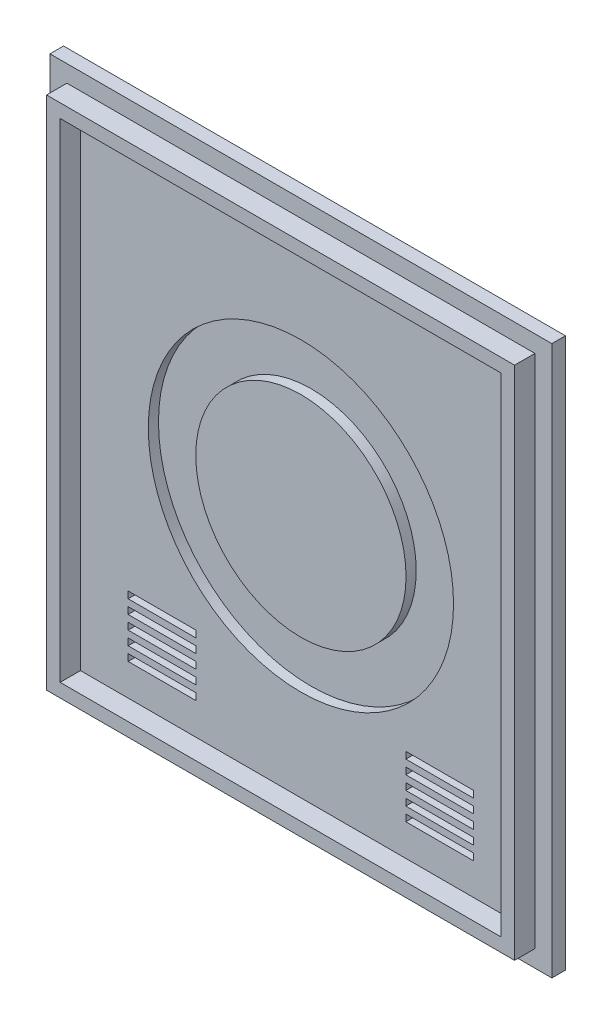
SolidWorks part; units mm, degrees
ref_plane "Ebene vorne" through (0, 0, 0) normal (0, 0, 1) x (1, 0, 0)
ref_plane "Ebene oben" through (0, 0, 0) normal (0, 1, 0) x (1, 0, 0)
ref_plane "Ebene rechts" through (0, 0, 0) normal (1, 0, 0) x (0, 0, -1)
sketch "Skizze1" plane through (0, 0, 0) normal (0, 0, 1) x (1, 0, 0)
  line L1 (-41.2602, 20.35) -> (32.7398, 20.35)
  line L2 (-41.2602, 20.35) -> (-41.2602, -60.65)
  line L3 (-41.2602, -60.65) -> (32.7398, -60.65)
  line L4 (32.7398, 20.35) -> (32.7398, -60.65)
  dimension "D1" = 74
  dimension "D2" = 81
extrude "Aufsatz-Linear austragen1" add sketch "Skizze1" along normal blind 2
sketch "Skizze2" plane through (0, 0, 2) normal (0, 0, 1) x (1, 0, 0)
  line L0 (-36.7602, 15.85) -> (-36.7602, -56.15)
  line L1 (-36.7602, -56.15) -> (28.2398, -56.15)
  line L2 (28.2398, -56.15) -> (28.2398, 15.85)
  line L3 (28.2398, 15.85) -> (-36.7602, 15.85)
  line L8 (-38.7602, 17.85) -> (-38.7602, -58.15)
  line L9 (-38.7602, -58.15) -> (30.2398, -58.15)
  line L10 (30.2398, -58.15) -> (30.2398, 17.85)
  line L11 (30.2398, 17.85) -> (-38.7602, 17.85)
  line L12 (-38.7602, 17.85) -> (-38.7602, -58.15)
  line L13 (-38.7602, -58.15) -> (30.2398, -58.15)
  line L14 (30.2398, -58.15) -> (30.2398, 17.85)
  line L15 (30.2398, 17.85) -> (-38.7602, 17.85)
  dimension "D1" = 2.5
  dimension "D2" = 2
extrude "Aufsatz-Linear austragen2" add sketch "Skizze2" along normal blind 3
sketch "Skizze3" plane through (0, 0, 2) normal (0, 0, 1) x (1, 0, 0)
  line L0 (28.2398, 15.85) -> (-36.7602, -56.15) construction
  line L1 (-36.7602, 15.85) -> (28.2398, -56.15) construction
  circle A0 centre (-4.2602, -20.15) radius 22.5
  circle A1 centre (-4.2602, -20.15) radius 15.5
  dimension "D1" = 45
  dimension "D2" = 7
extrude "Schnitt-Linear austragen3" cut sketch "Skizze3" against normal blind 1.5
sketch "Skizze4" plane through (0, 0, 2) normal (0, 0, 1) x (1, 0, 0)
  line L0 (-29.7317, -49.4683) -> (-29.7317, -48.4683)
  line L1 (-29.7317, -51.4683) -> (-19.7317, -51.4683)
  line L2 (-29.7317, -51.4683) -> (-29.7317, -50.4683)
  line L3 (-29.7317, -50.4683) -> (-19.7317, -50.4683)
  line L4 (-19.7317, -51.4683) -> (-19.7317, -50.4683)
  line L5 (-29.7317, -49.4683) -> (-19.7317, -49.4683)
  line L6 (-19.7317, -49.4683) -> (-19.7317, -48.4683)
  line L7 (-29.7317, -48.4683) -> (-19.7317, -48.4683)
  line L8 (-29.7317, -47.4683) -> (-29.7317, -46.4683)
  line L9 (-29.7317, -47.4683) -> (-19.7317, -47.4683)
  line L10 (-19.7317, -47.4683) -> (-19.7317, -46.4683)
  line L11 (-29.7317, -46.4683) -> (-19.7317, -46.4683)
  line L12 (-29.7317, -45.4683) -> (-29.7317, -44.4683)
  line L13 (-29.7317, -45.4683) -> (-19.7317, -45.4683)
  line L14 (-19.7317, -45.4683) -> (-19.7317, -44.4683)
  line L15 (-29.7317, -44.4683) -> (-19.7317, -44.4683)
  line L16 (-29.7317, -43.4683) -> (-29.7317, -42.4683)
  line L17 (-29.7317, -43.4683) -> (-19.7317, -43.4683)
  line L18 (-19.7317, -43.4683) -> (-19.7317, -42.4683)
  line L19 (-29.7317, -42.4683) -> (-19.7317, -42.4683)
  dimension "D1" = 1
  dimension "D2" = 10
  dimension "D3" = 5
extrude "Schnitt-Linear austragen4" cut sketch "Skizze4" against normal through all contours L2 L1 L4 L3 | L0 L7 L6 L5 | L12 L15 L14 L13 | L8 L11 L10 L9 | L16 L19 L18 L17
sketch "Skizze5" plane through (0, 0, 2) normal (0, 0, 1) x (1, 0, 0)
  line L1 (11.2098, -50.4683) -> (21.2098, -50.4683)
  line L2 (11.2098, -50.4683) -> (11.2098, -51.4683)
  line L3 (11.2098, -51.4683) -> (21.2098, -51.4683)
  line L4 (21.2098, -50.4683) -> (21.2098, -51.4683)
  line L6 (-29.7317, -51.4683) -> (-19.7317, -51.4683) construction
  line L9 (-36.7602, 15.85) -> (-36.7602, -56.15) construction
  line L10 (-36.7602, 15.85) -> (-36.7602, -56.15) construction
  line L12 (28.2398, -56.15) -> (28.2398, 15.85) construction
  line L13 (11.2098, -48.4683) -> (11.2098, -49.4683)
  line L14 (11.2098, -48.4683) -> (21.2098, -48.4683)
  line L15 (21.2098, -48.4683) -> (21.2098, -49.4683)
  line L16 (11.2098, -49.4683) -> (21.2098, -49.4683)
  line L17 (11.2098, -46.4683) -> (11.2098, -47.4683)
  line L18 (11.2098, -46.4683) -> (21.2098, -46.4683)
  line L19 (21.2098, -46.4683) -> (21.2098, -47.4683)
  line L20 (11.2098, -47.4683) -> (21.2098, -47.4683)
  line L21 (11.2098, -44.4683) -> (11.2098, -45.4683)
  line L22 (11.2098, -44.4683) -> (21.2098, -44.4683)
  line L23 (21.2098, -44.4683) -> (21.2098, -45.4683)
  line L24 (11.2098, -45.4683) -> (21.2098, -45.4683)
  line L25 (11.2098, -42.4683) -> (11.2098, -43.4683)
  line L26 (11.2098, -42.4683) -> (21.2098, -42.4683)
  line L27 (21.2098, -42.4683) -> (21.2098, -43.4683)
  line L28 (11.2098, -43.4683) -> (21.2098, -43.4683)
  dimension "D1" = 10
  dimension "D2" = 1
  dimension "D3" = 7.03
  dimension "D4" = 5
extrude "Schnitt-Linear austragen5" cut sketch "Skizze5" against normal through all
